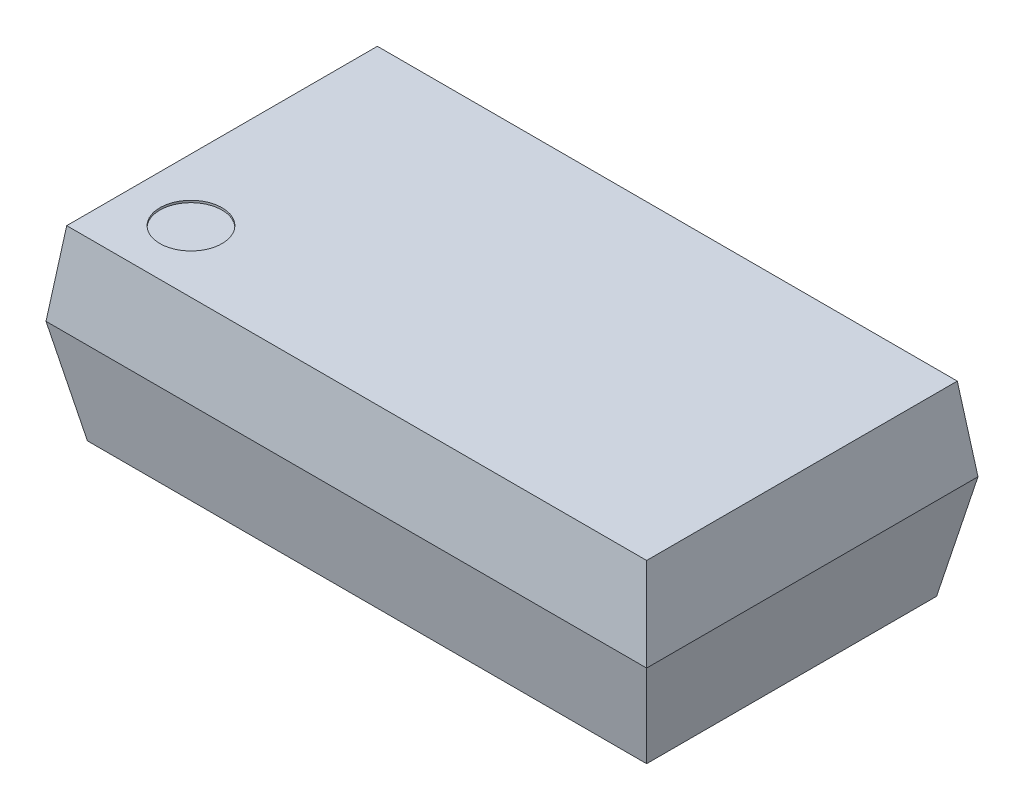
SolidWorks part; units mm, degrees
ref_plane "Front Plane" through (0, 0, 0) normal (0, 0, 1) x (1, 0, 0)
ref_plane "Top Plane" through (0, 0, 0) normal (0, 1, 0) x (1, 0, 0)
ref_plane "Right Plane" through (0, 0, 0) normal (1, 0, 0) x (0, 0, -1)
sketch "Sketch1" plane through (0, 0, 0) normal (0, 1, 0) x (1, 0, 0)
  line L1 (-1.45, -0.8) -> (1.45, -0.8)
  line L2 (-1.45, -0.8) -> (-1.45, 0.8)
  line L3 (-1.45, 0.8) -> (1.45, 0.8)
  line L4 (1.45, -0.8) -> (1.45, 0.8)
  line L5 (-1.45, -0.8) -> (1.45, 0.8) construction
  line L6 (-1.45, 0.8) -> (1.45, -0.8) construction
  point P0 (0, 0)
  dimension "D1" = 2.9
  dimension "D2" = 1.6
extrude "Boss-Extrude1" add sketch "Sketch1" along normal blind 0.9
sketch "Sketch2" plane through (0, 0, 0) normal (1, 0, 0) x (0, 0, -1)
  line L0 (-0.8, 0.5) -> (-0.7, 0)
  line L1 (-0.8, 0.9) -> (-0.8, 0) construction
  line L2 (0.8, 0) -> (-0.8, 0) construction
  line L3 (-0.7, 0) -> (-0.8, 0)
  line L4 (-0.8, 0) -> (-0.8, 0.5)
  dimension "D1" = 0.5
  dimension "D2" = 0.1
extrude "Cut-Extrude1" cut sketch "Sketch2" against normal through all both and the other way through all
mirror "Mirror1" about plane through (0, 0, 0) normal (0, 0, 1) of "Cut-Extrude1"
sketch "Sketch3" plane through (0, 0, 0) normal (1, 0, 0) x (0, 0, -1)
  line L0 (-0.8, 0.5) -> (-0.75, 0.9)
  line L1 (0.8, 0.9) -> (-0.8, 0.9) construction
  line L2 (-0.75, 0.9) -> (-0.8, 0.9)
  line L3 (-0.8, 0.9) -> (-0.8, 0.5)
  dimension "D1" = 0.05
extrude "Cut-Extrude2" cut sketch "Sketch3" against normal through all both and the other way through all
mirror "Mirror2" about plane through (0, 0, 0) normal (0, 0, 1) of "Cut-Extrude2"
sketch "Sketch4" plane through (0, 0, 0) normal (0, 0, 1) x (1, 0, 0)
  line L0 (-1.45, 0.5) -> (-1.35, 0)
  line L1 (-1.45, 0) -> (1.45, 0) construction
  line L2 (-1.35, 0) -> (-1.45, 0)
  line L3 (-1.45, 0) -> (-1.45, 0.5)
  dimension "D1" = 0.1
extrude "Cut-Extrude3" cut sketch "Sketch4" against normal through all both and the other way through all
mirror "Mirror3" about plane through (0, 0, 0) normal (1, 0, 0) of "Cut-Extrude3"
sketch "Sketch5" plane through (0, 0, 0) normal (0, 0, 1) x (1, 0, 0)
  line L0 (-1.45, 0.5) -> (-1.4, 0.9)
  line L1 (-1.45, 0.9) -> (1.45, 0.9) construction
  line L2 (-1.4, 0.9) -> (-1.45, 0.9)
  line L3 (-1.45, 0.9) -> (-1.45, 0.5)
  dimension "D1" = 0.05
extrude "Cut-Extrude4" cut sketch "Sketch5" against normal through all both and the other way through all
mirror "Mirror4" about plane through (0, 0, 0) normal (1, 0, 0) of "Cut-Extrude4"
sketch "Sketch6" plane through (0, 0.9, 0) normal (0, 1, 0) x (1, 0, 0)
  line L0 (-1.4, 0.75) -> (-1.4, -0.75) construction
  line L1 (-1.4, -0.75) -> (1.4, -0.75) construction
  circle A0 centre (-1.1, -0.45) radius 0.15
  dimension "D3" = 0.3
  dimension "D1" = 0.3
  dimension "D2" = 0.3
extrude "Cut-Extrude5" cut sketch "Sketch6" against normal blind 0.01
